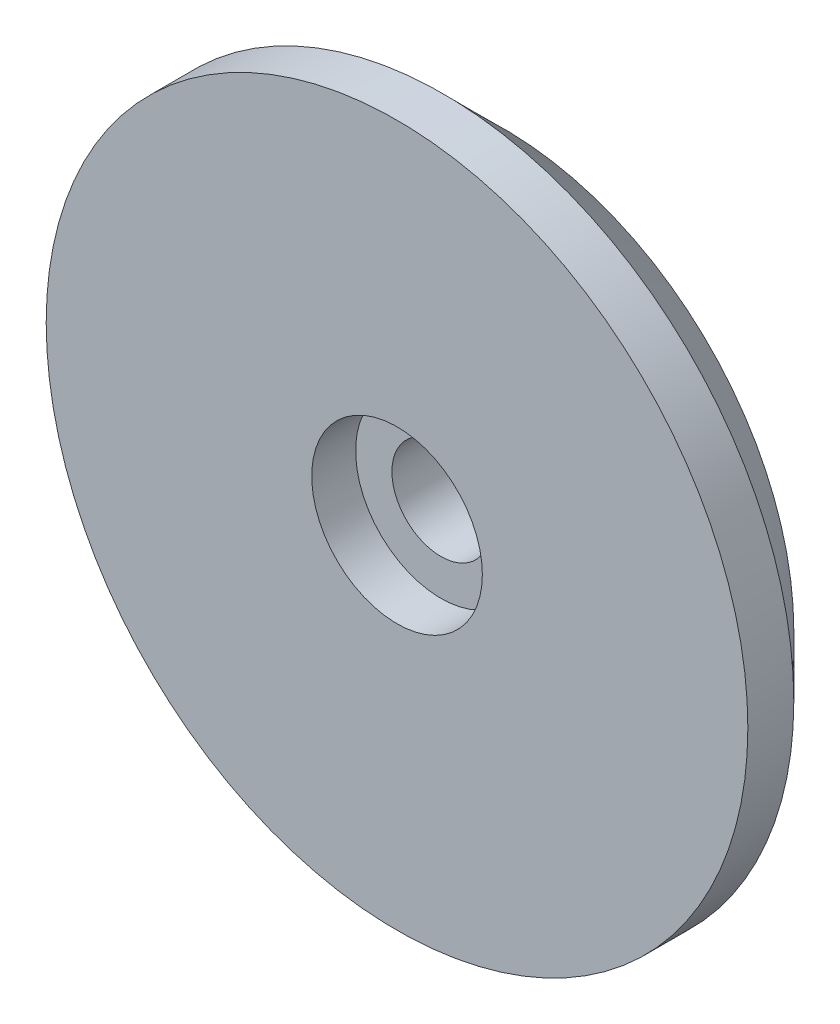
SolidWorks part; units mm, degrees
ref_plane "Front Plane" through (0, 0, 0) normal (0, 0, 1) x (1, 0, 0)
ref_plane "Top Plane" through (0, 0, 0) normal (0, 1, 0) x (1, 0, 0)
ref_plane "Right Plane" through (0, 0, 0) normal (1, 0, 0) x (0, 0, -1)
sketch "Sketch2" plane through (0, 0, -466.7752) normal (0, 0, 1) x (1, 0, 0)
  circle A0 centre (0, 0) radius 17.1812
extrude "Boss-Extrude1" add sketch "Sketch2" along normal blind 1.25 and the other way blind 4
sketch "Sketch3" plane through (0, 0, -470.7752) normal (0, 0, -1) x (-1, 0, 0)
  circle A0 centre (0, 0) radius 5.6298
  circle A1 centre (0, 0) radius 14.0791
extrude "Cut-Extrude1" cut sketch "Sketch3" against normal blind 2.25
sketch "Sketch4" plane through (0, 0, -470.7752) normal (0, 0, -1) x (-1, 0, 0)
  circle A0 centre (0, 0) radius 2.4
  dimension "D1" = 4.8
extrude "Cut-Extrude2" cut sketch "Sketch4" against normal blind 12.25
sketch "Sketch5" plane through (0, 0, -465.5252) normal (0, 0, 1) x (1, 0, 0)
  circle A0 centre (0, 0) radius 4.1787
extrude "Cut-Extrude3" cut sketch "Sketch5" against normal blind 2.15
chamfer "Chamfer1" distance 3 angle 45 1 edges at (17.1812, 0, -470.7752)
scale "Scale2" scale about centroid uniform scaling yes scale factor 0.75
